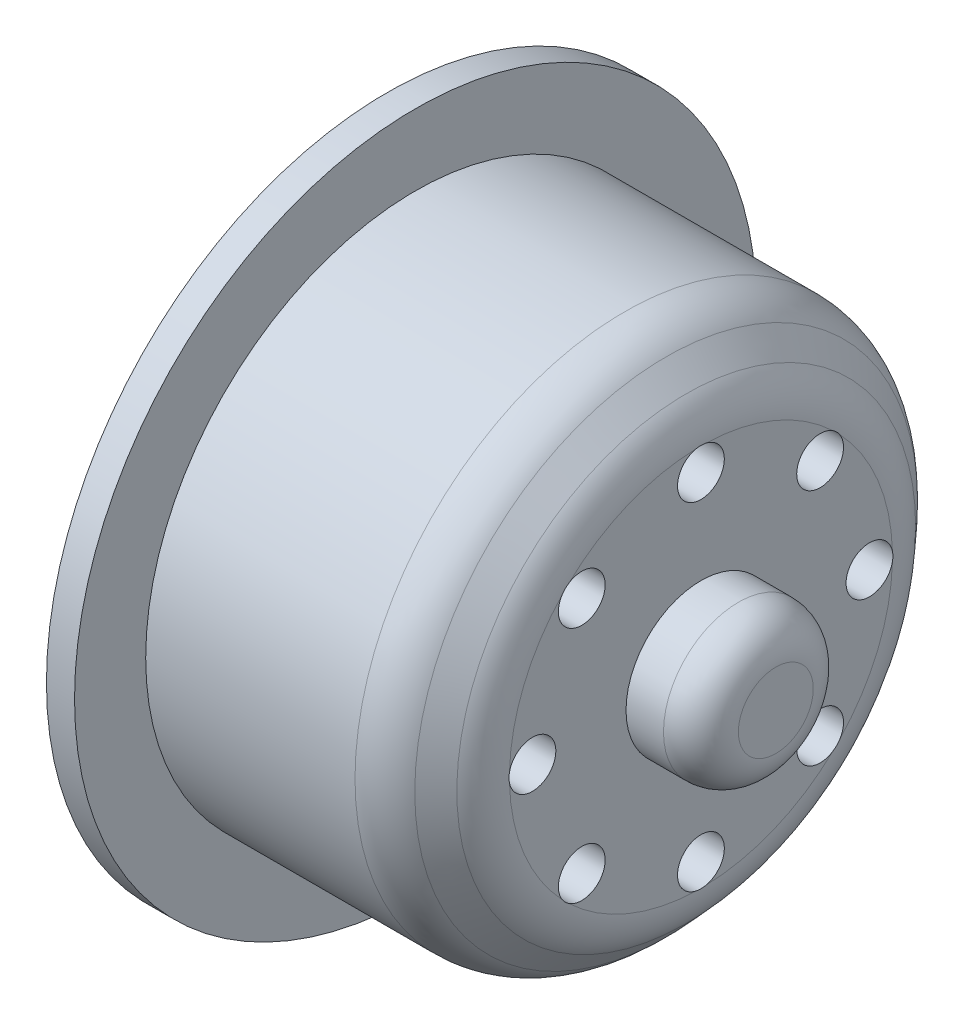
SolidWorks part; units mm, degrees
ref_plane "Front Plane" through (0, 0, 0) normal (0, 0, 1) x (1, 0, 0)
ref_plane "Top Plane" through (0, 0, 0) normal (0, 1, 0) x (1, 0, 0)
ref_plane "Right Plane" through (0, 0, 0) normal (1, 0, 0) x (0, 0, -1)
sketch "Sketch1" plane through (0, 0, 0) normal (0, 1, 0) x (1, 0, 0)
  line L0 (-12.3913, 0) -> (21, 0) construction
  line L1 (-4.6304, 14.4) -> (7.8696, 14.4)
  line L5 (13.3727, 0) -> (-6.1304, 0)
  line L8 (10.6196, 4) -> (14.6196, 4)
  line L9 (14.6196, 4) -> (14.6196, 0)
  line L10 (14.6196, 0) -> (13.3727, 0)
  line L11 (-4.6304, 14.4) -> (-4.6304, 18.2)
  line L12 (-4.6304, 18.2) -> (-6.1304, 18.2)
  line L13 (-6.1304, 18.2) -> (-6.1304, 0)
  line L15 (7.8696, 14.4) -> (10.6196, 11.3905)
  line L17 (10.6196, 11.3905) -> (10.6196, 4)
  dimension "D2" = 132.42
  dimension "D3" = 4.0767
  dimension "D4" = 12.5
  dimension "D5" = 28.8
  dimension "D6" = 3.0095
  dimension "D7" = 4
  dimension "D8" = 8
  dimension "D9" = 3.8
  dimension "D10" = 1.5
  dimension "D11" = 11.3905
revolve "Revolve1" add sketch "Sketch1" angle 360 about L0
fillet "Fillet1" radius 2 1 edges at (14.6196, 0, 4)
sketch "Sketch4" plane through (-6.1304, 0, 0) normal (-1, 0, 0) x (0, 0, 1)
  circle A0 centre (0, 0) radius 5.6
  dimension "D1" = 11.2
extrude "Cut-Extrude3" cut sketch "Sketch4" against normal blind 6
sketch "Sketch5" plane through (10.6196, 0, 0) normal (1, 0, 0) x (0, 0, -1)
  circle A0 centre (0, 0) radius 9 construction
  circle A1 centre (0, 9) radius 1.25
  circle A2 centre (6.364, 6.364) radius 1.25
  circle A3 centre (9, 0) radius 1.25
  circle A4 centre (6.364, -6.364) radius 1.25
  circle A5 centre (0, -9) radius 1.25
  circle A6 centre (-6.364, -6.364) radius 1.25
  circle A7 centre (-9, 0) radius 1.25
  circle A8 centre (-6.364, 6.364) radius 1.25
  point P22 (0, 0)
  dimension "D1" = 18
  dimension "D2" = 2.5
  dimension "D3" = 8
extrude "Cut-Extrude4" cut sketch "Sketch5" against normal up to surface (16.75 mm away) up to face at (-6.1304, 0, 5.6)
sketch "Sketch6" plane through (-6.1304, 0, 0) normal (-1, 0, 0) x (0, 0, 1)
  circle A0 centre (0, 0) radius 9 construction
  circle A1 centre (0, 9) radius 2.5
  circle A2 centre (6.364, 6.364) radius 2.5
  circle A3 centre (9, 0) radius 2.5
  circle A4 centre (6.364, -6.364) radius 2.5
  circle A5 centre (0, -9) radius 2.5
  circle A6 centre (-6.364, -6.364) radius 2.5
  circle A7 centre (-9, 0) radius 2.5
  circle A8 centre (-6.364, 6.364) radius 2.5
  point P22 (0, 0)
  dimension "D1" = 18
  dimension "D2" = 5
  dimension "D3" = 8
extrude "Cut-Extrude5" cut sketch "Sketch6" against normal offset from surface (11.75 mm away) 5 up to face at (10.6196, 9, -1.25)
fillet "Fillet2" radius 3 2 edges at (10.6196, 0, 11.3905) (7.8696, 0, 14.4)
